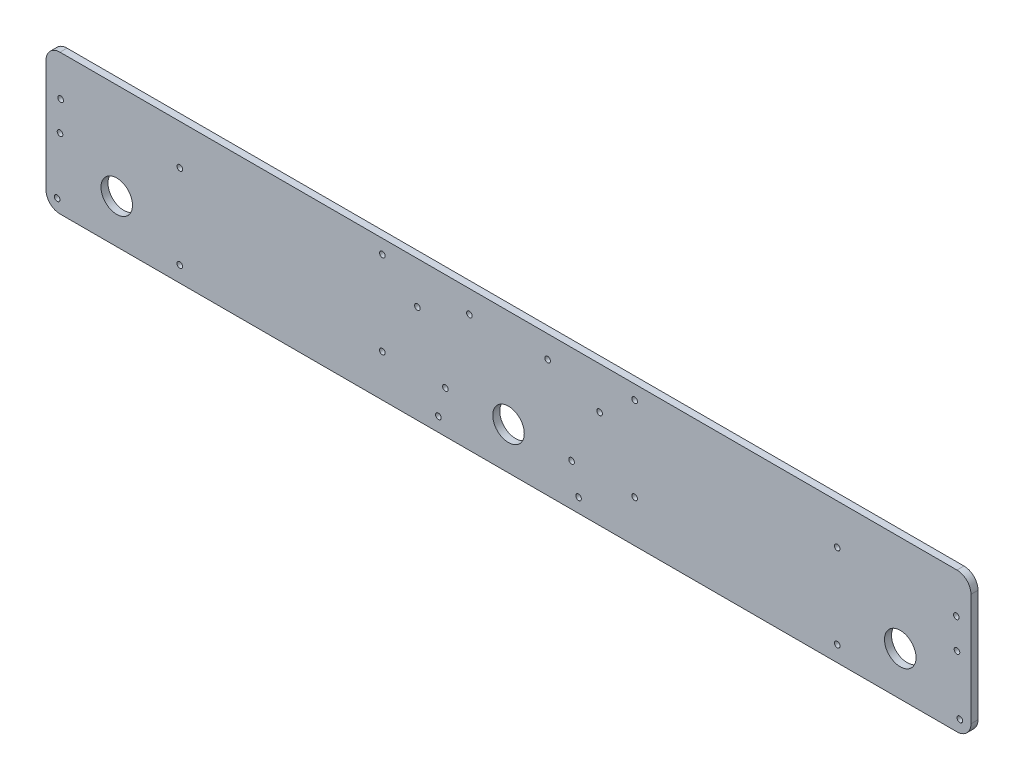
SolidWorks part; units mm, degrees
ref_plane "Front Plane" through (0, 0, 0) normal (0, 0, 1) x (1, 0, 0)
ref_plane "Top Plane" through (0, 0, 0) normal (0, 1, 0) x (1, 0, 0)
ref_plane "Right Plane" through (0, 0, 0) normal (1, 0, 0) x (0, 0, -1)
sketch "Sketch1" plane through (0, 0, 0) normal (0, 0, 1) x (1, 0, 0)
  line L1 (-419.1, -57.15) -> (419.1, -57.15)
  line L2 (419.1, 69.85) -> (-419.1, 69.85)
  line L4 (419.1, 69.85) -> (419.1, -57.15)
  line L6 (-419.1, 69.85) -> (-419.1, -57.15)
  point P0 (0, 0)
extrude "Boss-Extrude1" add sketch "Sketch1" along normal blind 6.35
sketch "Sketch2" plane through (0, 0, 6.35) normal (0, 0, 1) x (1, 0, 0)
  circle A0 centre (0, -19.05) radius 14.2875
extrude "Cut-Extrude1" cut sketch "Sketch2" against normal blind 6.35
sketch "Sketch3" plane through (0, 0, 6.35) normal (0, 0, 1) x (1, 0, 0)
  circle A0 centre (-354.998, -17.4625) radius 14.2875
  circle A1 centre (354.998, -17.4625) radius 14.2875
extrude "Cut-Extrude2" cut sketch "Sketch3" against normal blind 6.35
sketch "Sketch4" plane through (0, 0, 6.35) normal (0, 0, 1) x (1, 0, 0)
  circle A0 centre (-35.4127, 49.5808) radius 2.5527
  circle A1 centre (-57.15, -19.05) radius 2.5527
  circle A2 centre (57.15, -19.05) radius 2.5527
  circle A3 centre (35.4127, 49.5808) radius 2.5527
extrude "Cut-Extrude3" cut sketch "Sketch4" against normal blind 6.35
sketch "Sketch5" plane through (0, 0, 6.35) normal (0, 0, 1) x (1, 0, 0)
  circle A0 centre (-405.798, 33.3375) radius 2.5527
  circle A1 centre (408.973, -46.0375) radius 2.5527
  circle A2 centre (405.798, 33.3375) radius 2.5527
  circle A3 centre (63.5, -44.45) radius 2.5527
  circle A4 centre (-63.5, -44.45) radius 2.5527
  circle A5 centre (-297.848, -42.8625) radius 2.5527
  circle A7 centre (297.848, -42.8625) radius 2.5527
  circle A8 centre (-408.973, -46.0375) radius 2.5527
  circle A10 centre (-297.848, 33.3375) radius 2.5527
  circle A11 centre (297.848, 33.3375) radius 2.5527
  circle A13 centre (82.55, 31.75) radius 2.5527
  circle A14 centre (-82.55, 31.75) radius 2.5527
extrude "Cut-Extrude4" cut sketch "Sketch5" against normal blind 6.35
fillet "Fillet3" radius 12.7 4 edges at (419.1, -57.15, 3.175) (419.1, 69.85, 3.175) (-419.1, 69.85, 3.175) (-419.1, -57.15, 3.175)
sketch "Sketch6" plane through (0, 0, 6.35) normal (0, 0, 1) x (1, 0, 0)
  circle A0 centre (-406.4, 6.35) radius 2.5527
  circle A1 centre (406.4, 6.35) radius 2.5527
  circle A2 centre (-114.3, 57.15) radius 2.5527
  circle A3 centre (-114.3, -19.05) radius 2.5527
  circle A4 centre (114.3, 57.15) radius 2.5527
  circle A5 centre (114.3, -19.05) radius 2.5527
extrude "Cut-Extrude5" cut sketch "Sketch6" against normal blind 6.35
